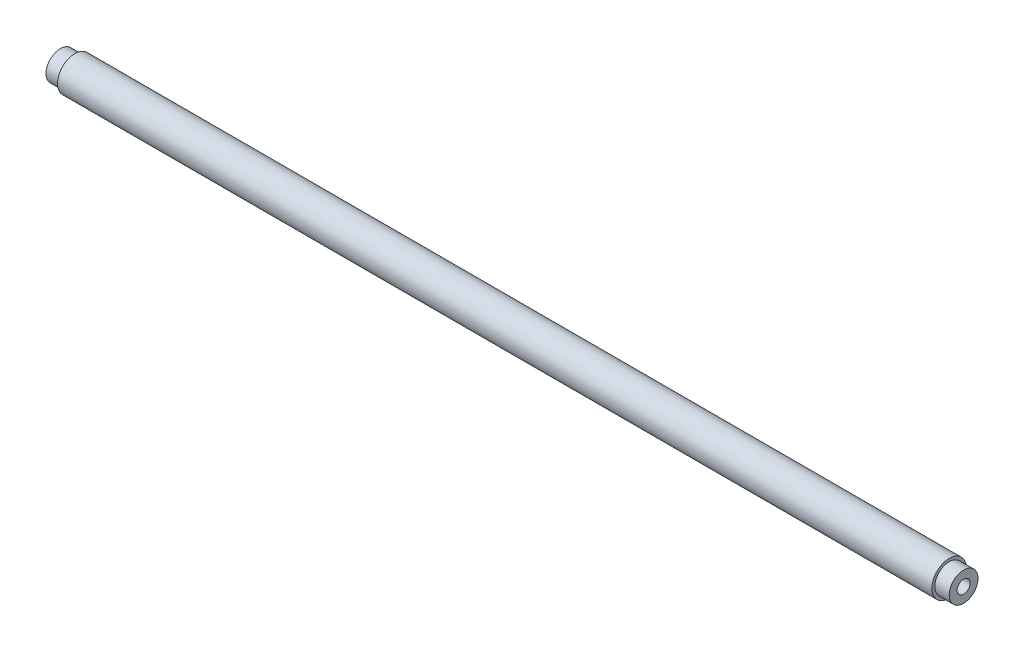
SolidWorks part; units mm, degrees
ref_plane "Front Plane" through (0, 0, 0) normal (0, 0, 1) x (1, 0, 0)
ref_plane "Top Plane" through (0, 0, 0) normal (0, 1, 0) x (1, 0, 0)
ref_plane "Right Plane" through (0, 0, 0) normal (1, 0, 0) x (0, 0, -1)
sketch "Çizim1" plane through (0, 0, 0) normal (0, 0, 1) x (1, 0, 0)
  line L0 (-235, 0) -> (235, 0)
  line L1 (-235, 0) -> (-235, 7.5)
  line L2 (-235, 7.5) -> (-227.5, 7.5)
  line L3 (-227.5, 7.5) -> (-227.5, 9)
  line L4 (-227.5, 9) -> (227.5, 9)
  line L5 (227.5, 9) -> (227.5, 7.5)
  line L6 (227.5, 7.5) -> (235, 7.5)
  line L7 (235, 7.5) -> (235, 0)
  point P4 (0, 0)
  dimension "D1" = 470
  dimension "D2" = 7.5
  dimension "D3" = 9
  dimension "D4" = 455
revolve "Döndür1" add sketch "Çizim1" angle 360 about L0
hole_wizard "M8 Dişli Delik1" positions "Çizim2" profile "Çizim3" tap size "M8" standard "ISO"
sketch "Çizim2" plane through (235, 0, 0) normal (1, 0, 0) x (0, 0, -1)
  point P0 (0, 0)
sketch "Çizim3" plane through (235, 0, 0) normal (0, 1, 0) x (0, 0, -1)
  line L0 (0, 0) -> (0, 22.0429)
  line L1 (0, 22.0429) -> (3.4, 20)
  line L2 (3.4, 20) -> (3.4, 0)
  line L5 (3.4, 0) -> (0, 0)
  line L10 (0, 22.0429) -> (-3.4, 20) construction
  line L11 (0, -6.35) -> (0, 107.95) construction
  dimension "Tap Drill Dia." = 6.8
  dimension "Tap Drill Depth" = 20
  dimension "Drill Angle" = 118
cosmetic thread "Delik Dişi1" parameters "D1"=16, "D2"=8
mirror "Aynalama1" about plane through (0, 0, 0) normal (1, 0, 0) of "M8 Dişli Delik1"
cosmetic thread "Delik Dişi2" parameters "D1"=16, "D2"=8
